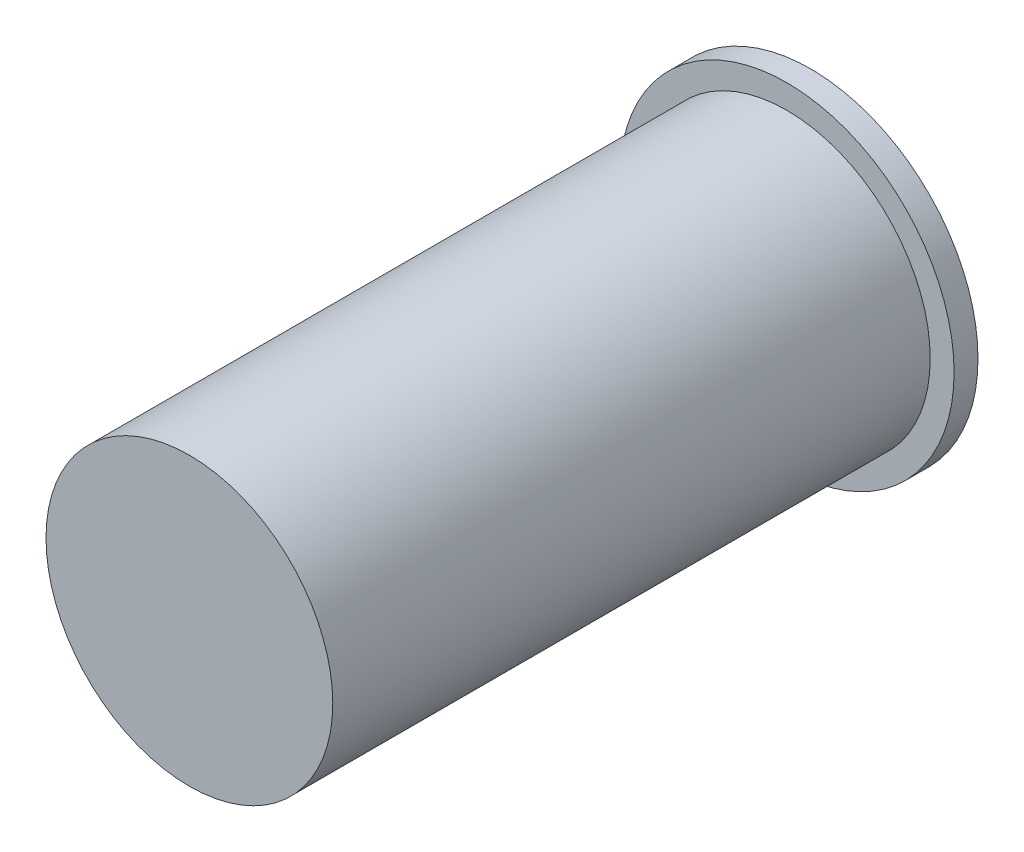
SolidWorks part; units mm, degrees
ref_plane "Front Plane" through (0, 0, 0) normal (0, 0, 1) x (1, 0, 0)
ref_plane "Top Plane" through (0, 0, 0) normal (0, 1, 0) x (1, 0, 0)
ref_plane "Right Plane" through (0, 0, 0) normal (1, 0, 0) x (0, 0, -1)
sketch "Sketch1" plane through (0, 0, 0) normal (0, 0, 1) x (1, 0, 0)
  circle A0 centre (-3.6793, 5.5121) radius 3.556
  point P2 (0, 0)
  dimension "D1" = 7.112
extrude "Boss-Extrude1" add sketch "Sketch1" along normal blind 0.508
sketch "Sketch4" plane through (0, 0, 0.508) normal (0, 0, 1) x (1, 0, 0)
  circle A0 centre (-3.6793, 5.5121) radius 3.048
  circle A1 centre (-3.6793, 5.5121) radius 3.556 construction
  dimension "D1" = 6.096
  dimension "D2" = 0
extrude "Boss-Extrude2" add sketch "Sketch4" along normal blind 12.7
